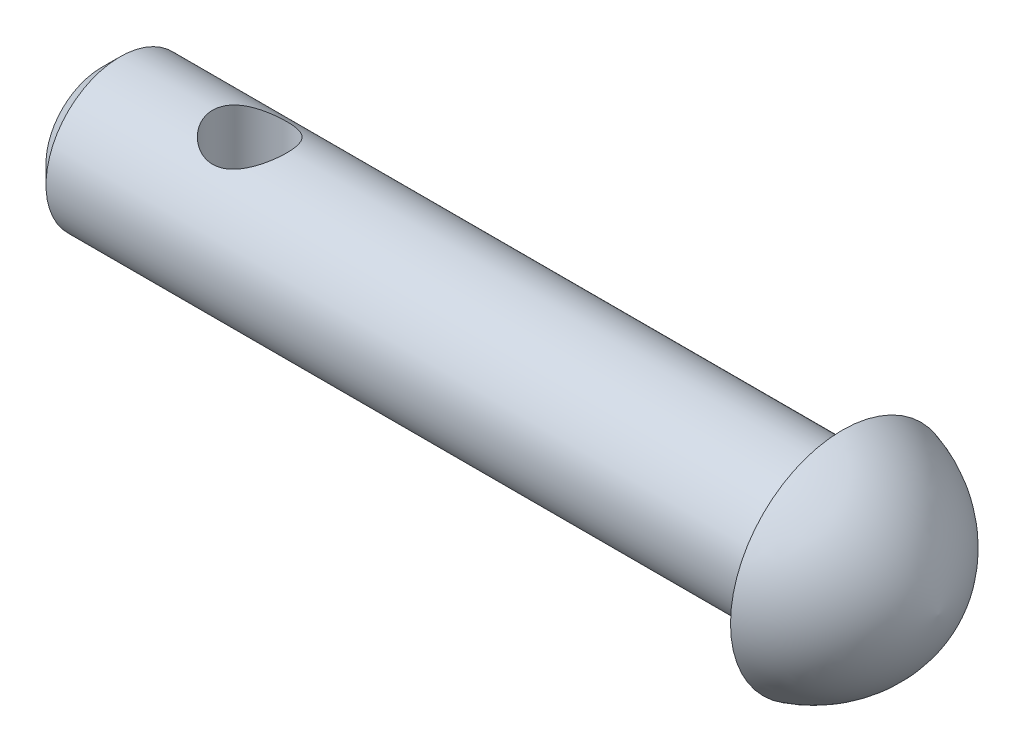
SolidWorks part; units mm, degrees
ref_plane "Front Plane" through (0, 0, 0) normal (0, 0, 1) x (1, 0, 0)
ref_plane "Top Plane" through (0, 0, 0) normal (0, 1, 0) x (1, 0, 0)
ref_plane "Right Plane" through (0, 0, 0) normal (1, 0, 0) x (0, 0, -1)
sketch "Sketch1" plane through (0, 0, 0) normal (1, 0, 0) x (0, 0, -1)
  circle A0 centre (0, 0) radius 2
extrude "Boss-Extrude1" add sketch "Sketch1" along normal blind 20
chamfer "Chamfer1" distance 0.5 angle 45 1 edges at (0, 0, -2)
sketch "Sketch2" plane through (0, 0, 0) normal (0, 1, 0) x (1, 0, 0)
  circle A0 centre (4, 0) radius 1
  dimension "D1" = 4
extrude "Cut-Extrude1" cut sketch "Sketch2" against normal through all both and the other way through all
sketch "Sketch4" plane through (0, 0, 0) normal (0, 0, 1) x (1, 0, 0)
  line L0 (19, 0) -> (22.6, 0) construction
  line L1 (20, -2) -> (20, 2) construction
  line L2 (20, 3.017) -> (20, 0)
  line L3 (22.6, 0) -> (20, 0)
  arc A0 (22.6, 0) -> (20, 3.017) centre (19.0282, -0.4493) ccw
  dimension "D1" = 1
  dimension "D2" = 3.6
revolve "Revolve1" add sketch "Sketch4" angle 360 about L0
